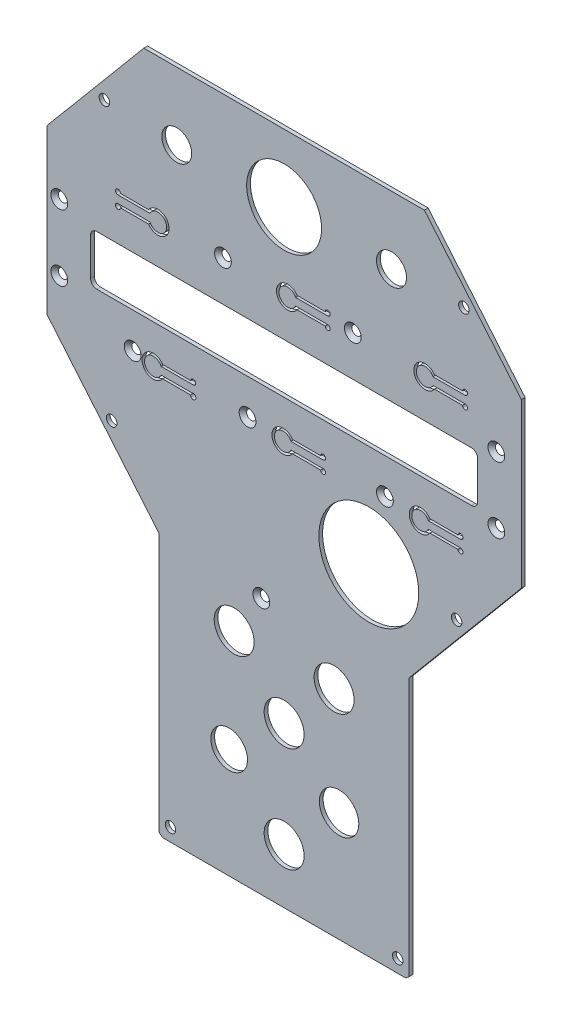
SolidWorks part; units mm, degrees
ref_plane "Plano frontal" through (0, 0, 0) normal (0, 0, 1) x (1, 0, 0)
ref_plane "Plano superior" through (0, 0, 0) normal (0, 1, 0) x (1, 0, 0)
ref_plane "Plano direito" through (0, 0, 0) normal (1, 0, 0) x (0, 0, -1)
sketch "Esboço1" plane through (0, 0, 0) normal (0, 0, 1) x (1, 0, 0)
  line L6 (55.321, 133.8096) -> (-57.007, 133.8096)
  line L7 (-57.007, 133.8096) -> (-95.843, 87.5267)
  line L8 (-95.843, 87.5267) -> (-95.843, 22.1402)
  line L9 (-95.843, 22.1402) -> (-50.843, -31.4887)
  line L10 (-50.843, -31.4887) -> (-50.843, -135.0827)
  line L11 (-50.843, -135.0827) -> (-49.5229, -136.1904)
  line L12 (-49.5229, -136.1904) -> (47.8369, -136.1904)
  line L13 (49.157, -135.0827) -> (47.8369, -136.1904)
  line L14 (49.157, -31.4887) -> (49.157, -135.0827)
  line L15 (94.157, 22.1402) -> (49.157, -31.4887)
  line L16 (94.157, 87.5267) -> (94.157, 22.1402)
  line L17 (55.321, 133.8096) -> (94.157, 87.5267)
  point P16 (-0.843, -136.1904)
  point P17 (-0.843, 133.8096)
extrude "Ressalto-extrusão1" add sketch "Esboço1" along normal blind 1.5
sketch "Esboço2" plane through (0, 0, 1.5) normal (0, 0, 1) x (1, 0, 0)
  line L0 (-0.843, -146.6722) -> (-0.843, 180.0647) construction
  line L1 (-95.843, 87.5267) -> (-95.843, 22.1402) construction
  line L2 (55.321, 133.8096) -> (-57.007, 133.8096) construction
  line L3 (-95.843, 22.1402) -> (-50.843, -31.4887) construction
  line L6 (49.157, -135.0827) -> (49.157, -31.4887) construction
  line L7 (-49.5229, -136.1904) -> (47.8369, -136.1904) construction
  line L9 (-50.843, -31.4887) -> (-50.843, -135.0827) construction
  circle A0 centre (-72.8144, 107.9499) radius 2.1
  circle A1 centre (-46.343, -130.9644) radius 2.1
  circle A2 centre (44.657, -130.9644) radius 2.1
  circle A3 centre (71.1284, 107.9499) radius 2.1
  circle A4 centre (-69.8958, -1.7817) radius 2.1
  circle A5 centre (68.2098, -1.7817) radius 2.1
  dimension "D1" = 23.0286
  dimension "D2" = 4.5
  dimension "D3" = 4.5
  dimension "D7" = 25.8597
  dimension "D4" = 5.226
  dimension "D11" = 4.5
extrude "Corte-extrusão1" cut sketch "Esboço2" against normal up to next
sketch "Esboço3" plane through (0, 0, 1.5) normal (0, 0, 1) x (1, 0, 0)
  line L0 (-95.843, 87.5267) -> (-95.843, 22.1402) construction
  line L1 (-49.5229, -136.1904) -> (47.8369, -136.1904) construction
  line L2 (-75.843, 40.8096) -> (74.157, 40.8096)
  line L3 (-78.343, 43.3096) -> (-78.343, 58.3096)
  line L4 (-75.843, 60.8096) -> (74.157, 60.8096)
  line L5 (76.657, 43.3096) -> (76.657, 58.3096)
  line L6 (-78.343, 40.8096) -> (76.657, 60.8096) construction
  line L7 (-78.343, 60.8096) -> (76.657, 40.8096) construction
  arc A0 (74.157, 60.8096) -> (76.657, 58.3096) centre (74.157, 58.3096) cw
  arc A1 (74.157, 40.8096) -> (76.657, 43.3096) centre (74.157, 43.3096) ccw
  arc A2 (-75.843, 40.8096) -> (-78.343, 43.3096) centre (-75.843, 43.3096) cw
  arc A3 (-78.343, 58.3096) -> (-75.843, 60.8096) centre (-75.843, 58.3096) cw
  dimension "D1" = 2.5
  dimension "D2" = 155
  dimension "D3" = 20
  dimension "D4" = 17.5
  dimension "D5" = 177
extrude "Corte-extrusão2" cut sketch "Esboço3" against normal up to next
sketch "Esboço4" plane through (0, 0, 1.5) normal (0, 0, 1) x (1, 0, 0)
  line L2 (-49.5229, -136.1904) -> (47.8369, -136.1904) construction
  line L3 (94.157, 22.1402) -> (94.157, 87.5267) construction
  circle A0 centre (33.0563, -0.1904) radius 20
  dimension "D1" = 136
  dimension "D2" = 61.1007
extrude "Corte-extrusão3" cut sketch "Esboço4" against normal up to next
sketch "Esboço5" plane through (0, 0, 1.5) normal (0, 0, 1) x (1, 0, 0)
  line L0 (-0.843, -136.1904) -> (-0.843, 252.6037) construction
  line L1 (-49.5229, -136.1904) -> (47.8369, -136.1904) construction
  line L2 (55.321, 133.8096) -> (-57.007, 133.8096) construction
  circle A0 centre (-0.843, -114.1904) radius 8
  circle A1 centre (-0.843, -72.1904) radius 8
  circle A2 centre (-22.843, -92.1904) radius 7.3454
  circle A3 centre (21.157, -92.1904) radius 7.8948
  circle A4 centre (-20.843, -50.1904) radius 8
  circle A5 centre (19.157, -50.1904) radius 8
  circle A6 centre (-0.843, 106.8096) radius 15
  circle A7 centre (-43.843, 106.8096) radius 6
  circle A8 centre (42.157, 106.8096) radius 6
  dimension "D1" = 42
  dimension "D2" = 22
  dimension "D3" = 22
  dimension "D4" = 22
  dimension "D5" = 22
  dimension "D6" = 22
  dimension "D7" = 22
  dimension "D8" = 20
  dimension "D9" = 20
  dimension "D10" = 22
  dimension "D11" = 27
  dimension "D12" = 43
  dimension "D13" = 43
extrude "Corte-extrusão4" cut sketch "Esboço5" against normal up to next
sketch "Esboço10" plane through (0, 0, 1.5) normal (0, 0, 1) x (1, 0, 0)
  circle A0 centre (-61.4827, 26.6206) radius 1.75
  circle A1 centre (-15.4827, 26.6206) radius 1.75
  circle A2 centre (39.5173, 26.6206) radius 1.75
  circle A3 centre (84.131, 37.971) radius 1.6
  circle A4 centre (84.131, 64.471) radius 1.6
  circle A5 centre (-90.869, 64.471) radius 1.6
  circle A6 centre (-90.869, 37.971) radius 1.6
  circle A7 centre (-25.3465, 76.9851) radius 1.75
  circle A8 centre (26.6535, 76.9851) radius 1.75
  circle A9 centre (-9.9827, -33.3794) radius 1.75
hole_wizard "Escareado para parafuso Allen sextavado escareado de M32" positions "3DSketch3" profile "Esboço11" countersink size "M3" standard "ISO" end condition through all
sketch3d "3DSketch3"
  point P0 (-90.869, 64.471, 1.5)
  point P3 (-90.869, 37.971, 1.5)
  point P6 (-61.4827, 26.6206, 1.5)
  point P9 (-15.4827, 26.6206, 1.5)
  point P12 (39.5173, 26.6206, 1.5)
  point P15 (84.131, 37.971, 1.5)
  point P18 (84.131, 64.471, 1.5)
  point P21 (26.6535, 76.9851, 1.5)
  point P24 (-25.3465, 76.9851, 1.5)
  point P27 (-9.9827, -33.3794, 1.5)
sketch "Esboço11" plane through (-90.869, 64.471, 1.5) normal (1, 0, 0) x (0, -1, 0)
  line L0 (0, 0) -> (0, 1.5)
  line L1 (0, 1.5) -> (1.7, 1.5)
  line L2 (1.7, 1.5) -> (1.7, 1.66)
  line L3 (1.7, 1.66) -> (3.36, 0)
  line L5 (3.36, 0) -> (0, 0)
  line L6 (-1.7, 1.66) -> (-3.36, 0) construction
  line L11 (0, -6.35) -> (0, 107.95) construction
  dimension "Thru Hole Dia." = 3.4
  dimension "Thru Hole Depth" = 1.5
  dimension "Near C'Sink Dia." = 6.72
  dimension "Near C'Sink Angle" = 90
sketch "Esboço12" plane through (0, 0, 1.5) normal (0, 0, 1) x (1, 0, 0)
  line L0 (-75.843, 40.8096) -> (74.157, 40.8096) construction
  line L1 (74.157, 60.8096) -> (-75.843, 60.8096) construction
  line L2 (94.157, 22.1402) -> (94.157, 87.5267) construction
  line L3 (56.9296, 26.9096) -> (69.7673, 26.9096)
  line L5 (68.7673, 27.9096) -> (57.509, 27.9096)
  line L6 (56.9296, 23.9096) -> (69.7673, 23.9096)
  line L7 (1.9296, 26.9096) -> (14.7673, 26.9096)
  line L8 (68.7673, 22.9096) -> (57.509, 22.9096)
  line L9 (13.7673, 22.9096) -> (2.509, 22.9096)
  line L10 (13.7673, 27.9096) -> (2.509, 27.9096)
  line L11 (1.9296, 23.9096) -> (14.7673, 23.9096)
  line L12 (-50.0704, 26.9096) -> (-37.2327, 26.9096)
  line L13 (-38.3131, 22.9096) -> (-49.491, 22.9096)
  line L14 (-38.2327, 27.9096) -> (-49.491, 27.9096)
  line L15 (-50.0704, 23.9096) -> (-37.6418, 23.9096)
  line L25 (3.7693, 77.7596) -> (16.607, 77.7596)
  line L26 (58.7693, 77.7596) -> (71.607, 77.7596)
  line L27 (15.607, 78.7596) -> (4.3487, 78.7596)
  line L28 (3.7693, 74.7596) -> (16.607, 74.7596)
  line L29 (-54.5553, 77.7596) -> (-67.393, 77.7596)
  line L30 (15.607, 73.7596) -> (4.3487, 73.7596)
  line L31 (70.607, 78.7596) -> (59.3487, 78.7596)
  line L32 (58.7693, 74.7596) -> (71.607, 74.7596)
  line L34 (70.607, 73.7596) -> (59.3487, 73.7596)
  line L35 (-66.393, 78.7596) -> (-55.1346, 78.7596)
  line L36 (-54.5553, 74.7596) -> (-67.393, 74.7596)
  line L38 (-66.393, 73.7596) -> (-55.1346, 73.7596)
  arc A0 (57.509, 27.9096) -> (57.509, 22.9096) centre (53.7673, 25.4096) ccw
  circle A1 centre (39.5173, 26.6206) radius 3.36 construction
  arc A2 (14.7673, 23.9096) -> (13.7673, 22.9096) centre (14.7673, 22.9096) cw
  arc A3 (-49.491, 27.9096) -> (-49.491, 22.9096) centre (-53.2327, 25.4096) ccw
  arc A4 (-55.1346, 73.7596) -> (-55.1346, 78.7596) centre (-51.393, 76.2596) ccw
  arc A5 (4.3487, 78.7596) -> (4.3487, 73.7596) centre (0.607, 76.2596) ccw
  arc A6 (59.3487, 78.7596) -> (59.3487, 73.7596) centre (55.607, 76.2596) ccw
  arc A7 (56.9296, 26.9096) -> (56.9296, 23.9096) centre (53.7673, 25.4096) ccw
  arc A8 (69.7673, 26.9096) -> (68.7673, 27.9096) centre (69.7673, 27.9096) ccw
  arc A9 (68.7673, 22.9096) -> (69.7673, 23.9096) centre (69.7673, 22.9096) ccw
  arc A10 (14.7673, 26.9096) -> (13.7673, 27.9096) centre (14.7673, 27.9096) ccw
  arc A11 (2.509, 27.9096) -> (2.509, 22.9096) centre (-1.2327, 25.4096) ccw
  arc A12 (1.9296, 26.9096) -> (1.9296, 23.9096) centre (-1.2327, 25.4096) ccw
  arc A13 (-37.2327, 26.9096) -> (-38.2327, 27.9096) centre (-37.2327, 27.9096) ccw
  arc A14 (-37.6418, 23.9096) -> (-38.3131, 22.9096) centre (-37.2327, 22.9096) cw
  arc A17 (-50.0704, 26.9096) -> (-50.0704, 23.9096) centre (-53.2327, 25.4096) ccw
  arc A22 (16.607, 77.7596) -> (15.607, 78.7596) centre (16.607, 78.7596) ccw
  arc A23 (58.7693, 77.7596) -> (58.7693, 74.7596) centre (55.607, 76.2596) ccw
  arc A24 (3.7693, 77.7596) -> (3.7693, 74.7596) centre (0.607, 76.2596) ccw
  arc A25 (15.607, 73.7596) -> (16.607, 74.7596) centre (16.607, 73.7596) ccw
  arc A26 (71.607, 77.7596) -> (70.607, 78.7596) centre (71.607, 78.7596) ccw
  arc A27 (70.607, 73.7596) -> (71.607, 74.7596) centre (71.607, 73.7596) ccw
  arc A28 (-54.5553, 74.7596) -> (-54.5553, 77.7596) centre (-51.393, 76.2596) ccw
  arc A29 (-66.393, 78.7596) -> (-67.393, 77.7596) centre (-67.393, 78.7596) ccw
  arc A30 (-67.393, 74.7596) -> (-66.393, 73.7596) centre (-67.393, 73.7596) ccw
  dimension "D1" = 14.25
  dimension "D2" = 15.4
  dimension "D5" = 15.45
  dimension "D6" = 38.55
  dimension "D7" = 55
  dimension "D8" = 52
  dimension "D9" = 1
  dimension "D13" = 16
  dimension "D14" = 4.5
  dimension "D15" = 3.5
  dimension "D16" = 3.5
  dimension "D17" = 4.5
  dimension "D10" = 1
  dimension "D18" = 16
  dimension "D22" = 3.5
  dimension "D19" = 40.3897
  dimension "D33" = 4.5
  dimension "D38" = 4.5
  dimension "D42" = 1
  dimension "D39" = 3.5
  dimension "D44" = 16
  dimension "D46" = 4.5
  dimension "D47" = 3.5
  dimension "D45" = 16
  dimension "D50" = 4.5
  dimension "D51" = 3.5
  dimension "D52" = 16
  dimension "D21" = 52
  dimension "D11" = 3
  dimension "D12" = 1.5
  dimension "D20" = 55
  dimension "D23" = 16
  dimension "D40" = 3
  dimension "D41" = 1.5
  dimension "D43" = 1
extrude "Corte-extrusão5" cut sketch "Esboço12" against normal blind 10
